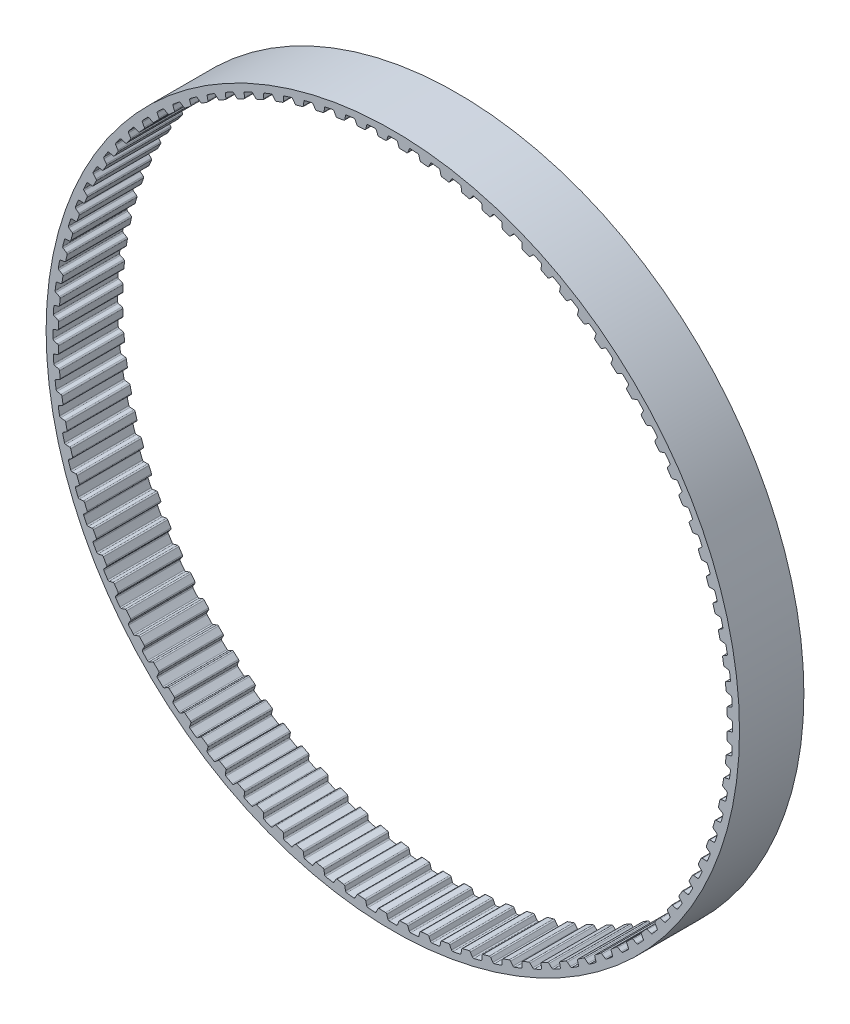
SolidWorks part; units mm, degrees
ref_plane "Front Plane" through (0, 0, 0) normal (0, 0, 1) x (1, 0, 0)
ref_plane "Top Plane" through (0, 0, 0) normal (0, 1, 0) x (1, 0, 0)
ref_plane "Right Plane" through (0, 0, 0) normal (1, 0, 0) x (0, 0, -1)
sketch "Sketch1" plane through (0, 0, 0) normal (0, 0, 1) x (1, 0, 0)
  line L0 (0, 0) -> (-0.9789, 31.1501) construction
  line L1 (0, 0) -> (0.9789, 31.1501) construction
  line L2 (0.9789, 31.1501) -> (-0.9789, 31.1501) construction
  line L3 (0.9789, 31.1501) -> (-0.9789, 31.1501) construction
  circle A0 centre (0, 0) radius 32.3085
  circle A1 centre (0, 0) radius 31.1655
  circle A2 centre (0, 0) radius 31.6735 construction
  dimension "OD" = 64.617
  dimension "Angle Distance" = 3.6
  dimension "hs" = 1.143
  dimension "ht" = 0.508
sketch "Sketch4" plane through (0, 0, 0) normal (0, 0, 1) x (1, 0, 0)
  circle A0 centre (0, 0) radius 31.1655 construction
  circle A1 centre (0, 0) radius 32.3085 construction
  circle A2 centre (0, 0) radius 31.1655
  circle A3 centre (0, 0) radius 32.3085
extrude "Boss-Extrude1" add sketch "Sketch4" along normal mid plane 6
sketch "Sketch2" plane through (0, 0, 0) normal (0, 0, 1) x (1, 0, 0)
  line L1 (0, 32.3085) -> (0, 0) construction
  line L2 (-1.015, 31.4165) -> (1.015, 31.4165) construction
  line L4 (-0.5904, 31.1623) -> (-1.3675, 31.1379)
  line L5 (-0.5904, 31.1623) -> (-0.4232, 31.6707)
  line L6 (-1.3675, 31.1379) -> (-1.5662, 31.6347)
  line L7 (0, 0) -> (-0.9789, 31.1501) construction
  line L8 (-0.4232, 31.6707) -> (-1.5662, 31.6347) construction
  line L9 (0.4232, 31.6707) -> (1.5662, 31.6347) construction
  line L10 (1.3675, 31.1379) -> (1.5662, 31.6347)
  line L11 (0.5904, 31.1623) -> (0.4232, 31.6707)
  line L12 (0.5904, 31.1623) -> (1.3675, 31.1379)
  line L13 (0, 0) -> (12.3639, 29.8491) construction
  line L14 (-1.015, 31.4165) -> (-3.0408, 31.2855) construction
  line L15 (-2.0279, 31.351) -> (0, 0) construction
  line L16 (-3.0408, 31.2855) -> (-3.0149, 31.0193) construction
  circle A0 centre (0, 0) radius 31.6735 construction
  circle A1 centre (0, 0) radius 31.6735
  circle A2 centre (0, 0) radius 31.4165 construction
  circle A4 centre (0, 0) radius 32.3085 construction
  circle A5 centre (0, 0) radius 31.1655 construction
  point P16 (-0.5068, 31.4165)
  point P20 (0, 31.4165)
  dimension "D1" = 22.5
  dimension "bt" = 1.143
  dimension "b" = 40
  dimension "Pitch" = 2.03
sketch "Sketch3" plane through (0, 0, 0) normal (0, 0, 1) x (1, 0, 0)
  line L0 (-0.6809, 31.158) -> (0.6809, 31.158)
  line L2 (-0.5904, 31.1623) -> (-0.4232, 31.6707) construction
  line L3 (0.5904, 31.1623) -> (0.4232, 31.6707) construction
  line L5 (-0.5631, 31.2453) -> (-0.4516, 31.5844)
  line L7 (0.5631, 31.2453) -> (0.4516, 31.5844)
  arc A0 (0.5631, 31.2453) -> (0.6809, 31.158) centre (0.6837, 31.285) ccw
  circle A1 centre (0, 0) radius 31.6735 construction
  arc A2 (0.3323, 31.6717) -> (-0.3323, 31.6717) centre (0, 0) ccw
  arc A3 (-0.5631, 31.2453) -> (-0.6809, 31.158) centre (-0.6837, 31.285) cw
  arc A4 (0.4516, 31.5844) -> (0.3323, 31.6717) centre (0.3309, 31.5447) ccw
  arc A5 (-0.4516, 31.5844) -> (-0.3323, 31.6717) centre (-0.3309, 31.5447) cw
  circle A6 centre (0, 0) radius 31.1655 construction
  arc A7 (-0.6809, 31.158) -> (0.6809, 31.158) centre (0, 0) ccw construction
  dimension "ra" = 0.127
  dimension "rr" = 0.127
extrude "Cut-Extrude1" cut sketch "Sketch3" against normal mid plane 6
pattern_circular "CirPattern1" count 100 over 360 about axis through (0, 0, 0) along (0, 0, 1) of "Cut-Extrude1"
equation "\"D1@Cut-Extrude1\" = \"Width@Boss-Extrude1\""
